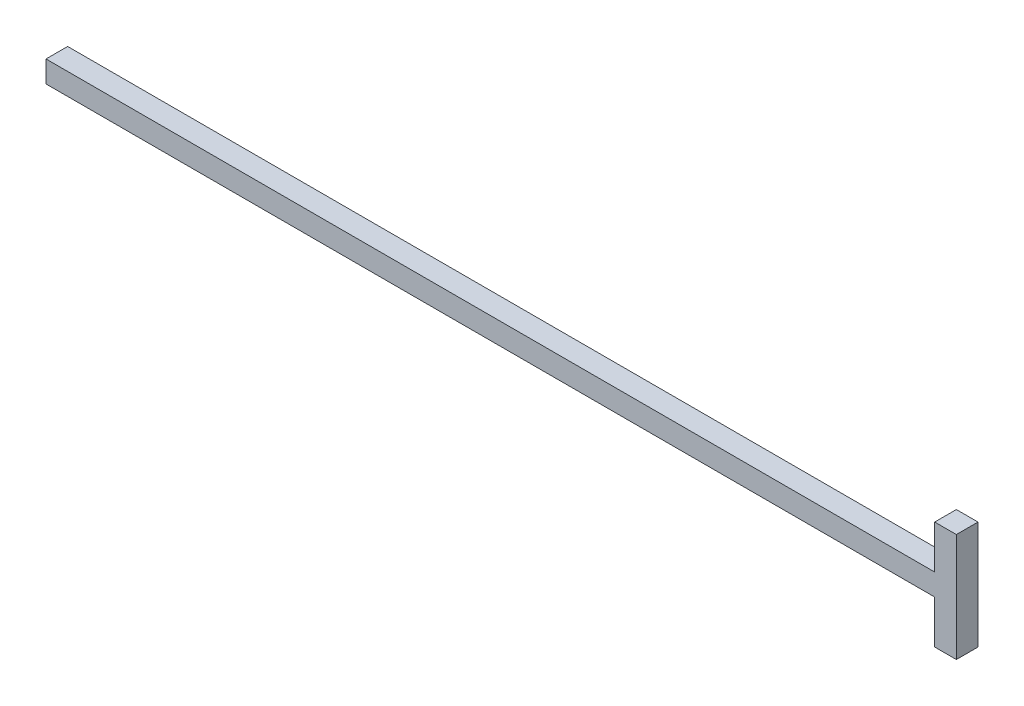
SolidWorks part; units mm, degrees
material "Acrylic (Medium-high impact)"
ref_plane "Front Plane" through (0, 0, 0) normal (0, 0, 1) x (1, 0, 0)
ref_plane "Top Plane" through (0, 0, 0) normal (0, 1, 0) x (1, 0, 0)
ref_plane "Right Plane" through (0, 0, 0) normal (1, 0, 0) x (0, 0, -1)
sketch "Sketch1" plane through (0, 0, 0) normal (0, 0, 1) x (1, 0, 0)
  line L1 (-133.477, 3.175) -> (133.477, 3.175)
  line L2 (-133.477, 3.175) -> (-133.477, -3.175)
  line L3 (-133.477, -3.175) -> (133.477, -3.175)
  line L4 (133.477, 3.175) -> (133.477, -3.175)
  line L5 (133.477, 3.175) -> (127.127, 3.175)
  line L6 (133.477, 3.175) -> (133.477, 15.875)
  line L7 (133.477, 15.875) -> (127.127, 15.875)
  line L8 (127.127, 3.175) -> (127.127, 15.875)
  line L9 (133.477, -3.175) -> (127.127, -3.175)
  line L10 (133.477, -3.175) -> (133.477, -15.875)
  line L11 (133.477, -15.875) -> (127.127, -15.875)
  line L12 (127.127, -3.175) -> (127.127, -15.875)
  point P4 (0, 3.175)
  point P6 (-133.477, 0)
  point P13 (138.0401, -17.8219)
  dimension "D1" = 6.35
  dimension "D2" = 6.35
  dimension "D3" = 6.35
  dimension "D4" = 12.7
  dimension "D5" = 260.604
extrude "Boss-Extrude1" add sketch "Sketch1" along normal blind 6.35 contours L4 L1 L2 L3 | L8 L1 L6 L7 | L3 L12 L11 L10
